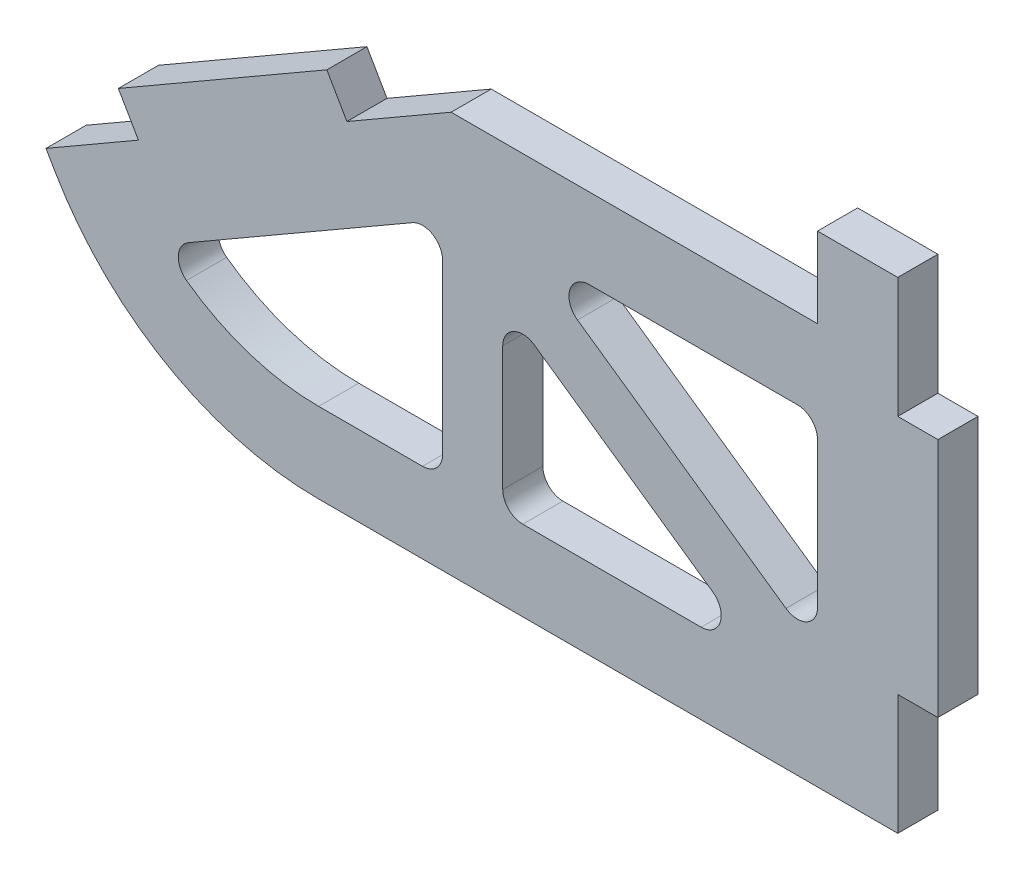
SolidWorks part; units mm, degrees
material "Plain Carbon Steel"
ref_plane "Front Plane" through (0, 0, 0) normal (0, 0, 1) x (1, 0, 0)
ref_plane "Top Plane" through (0, 0, 0) normal (0, 1, 0) x (1, 0, 0)
ref_plane "Right Plane" through (0, 0, 0) normal (1, 0, 0) x (0, 0, -1)
sketch "Sketch1" plane through (0, 0, 0) normal (0, 0, 1) x (1, 0, 0)
  line L1 (0, 0) -> (-152.4, 0)
  line L2 (0, 0) -> (0, -76.2)
  line L3 (0, -76.2) -> (-152.4, -76.2)
  line L4 (-152.4, 0) -> (-152.4, -76.2)
  dimension "D1" = 76.2
  dimension "D2" = 152.4
extrude "Boss-Extrude1" add sketch "Sketch1" along normal blind 6.35
sketch "Sketch2" plane through (0, 0, 6.35) normal (0, 0, 1) x (1, 0, 0)
  line L0 (0, -76.2) -> (0, 0) construction
  line L1 (0, -57.15) -> (6.35, -57.15)
  line L2 (0, -57.15) -> (0, -19.05)
  line L3 (0, -19.05) -> (6.35, -19.05)
  line L4 (6.35, -57.15) -> (6.35, -19.05)
  dimension "D1" = 6.35
  dimension "D2" = 38.1
  dimension "D3" = 19.05
extrude "Boss-Extrude2" add sketch "Sketch2" against normal blind 6.35
sketch "Sketch3" plane through (0, 0, 6.35) normal (0, 0, 1) x (1, 0, 0)
  line L0 (-152.4, -59.8789) -> (-70.6837, -12.7)
  line L1 (-152.4, 0) -> (-152.4, -76.2) construction
  line L3 (-70.6837, -12.7) -> (-12.7, -12.7)
  line L4 (-12.7, -12.7) -> (-12.7, 0)
  line L5 (0, 0) -> (-152.4, 0) construction
  line L6 (-12.7, 0) -> (-152.4, 0)
  line L7 (-152.4, 0) -> (-152.4, -59.8789)
  line L8 (0, -19.05) -> (0, 0) construction
  dimension "D1" = 12.7
  dimension "D2" = 12.7
extrude "Cut-Extrude1" cut sketch "Sketch3" against normal through all
sketch "Sketch4" plane through (0, 0, 6.35) normal (0, 0, 1) x (1, 0, 0)
  line L0 (-152.4, -59.8789) -> (-133.35, -76.2)
  line L1 (-152.4, -76.2) -> (0, -76.2) construction
  line L2 (-133.35, -76.2) -> (-152.4, -76.2)
  line L3 (-152.4, -76.2) -> (-152.4, -59.8789)
  dimension "D1" = 19.05
extrude "Cut-Extrude2" cut sketch "Sketch4" against normal through all
sketch "Sketch5" plane through (0, 0, 6.35) normal (0, 0, 1) x (1, 0, 0)
  line L0 (-87.1815, -22.225) -> (-90.3565, -16.7257)
  line L1 (-152.4, -59.8789) -> (-70.6837, -12.7) construction
  line L3 (-90.3565, -16.7257) -> (-123.3521, -35.7757)
  line L4 (-123.3521, -35.7757) -> (-120.1771, -41.275)
  line L5 (-120.1771, -41.275) -> (-87.1815, -22.225)
  dimension "D1" = 38.1
  dimension "D2" = 19.05
  dimension "D3" = 6.35
extrude "Boss-Extrude3" add sketch "Sketch5" against normal blind 6.35
sketch "Sketch6" plane through (0, 0, 6.35) normal (0, 0, 1) x (1, 0, 0)
  line L0 (-134.8024, -49.7189) -> (-119.5135, -76.2)
  line L1 (-152.4, -59.8789) -> (-120.1771, -41.275) construction
  line L2 (-119.5135, -76.2) -> (-133.35, -76.2)
  line L3 (-133.35, -76.2) -> (-152.4, -59.8789)
  line L4 (-152.4, -59.8789) -> (-134.8024, -49.7189)
  line L5 (-133.35, -76.2) -> (-152.4, -59.8789) construction
  line L6 (-133.35, -76.2) -> (0, -76.2) construction
  dimension "D1" = 20.32
extrude "Cut-Extrude3" cut sketch "Sketch6" against normal through all
fillet "Fillet1" radius 48.26 1 edges at (-119.5135, -76.2, 3.175)
sketch "Sketch7" plane through (0, 0, 6.35) normal (0, 0, 1) x (1, 0, 0)
  line L15 (-102.8286, -45.9235) -> (-91.83, -39.5735)
  line L16 (-12.7, -44.45) -> (-12.7, -31.75)
  line L30 (-91.6506, -63.5) -> (-12.7, -63.5)
  line L31 (-12.7, -63.5) -> (-12.7, -44.45)
  line L32 (-12.7, -44.45) -> (-6.35, -44.45)
  line L33 (-6.35, -44.45) -> (-6.35, -31.75)
  line L34 (-6.35, -31.75) -> (-12.7, -31.75)
  line L35 (-12.7, -31.75) -> (-12.7, -25.4)
  line L36 (-12.7, -25.4) -> (-67.2808, -25.4)
  line L37 (-67.2808, -25.4) -> (-91.83, -39.5735)
  line L38 (-91.83, -39.5735) -> (-95.005, -34.0743)
  line L39 (-95.005, -34.0743) -> (-106.0036, -40.4243)
  line L40 (-106.0036, -40.4243) -> (-102.8286, -45.9235)
  line L41 (-102.8286, -45.9235) -> (-116.2148, -53.6521)
  line L42 (-91.6506, -63.5) -> (-12.7, -63.5)
  line L43 (-12.7, -63.5) -> (-12.7, -44.45)
  line L47 (-12.7, -31.75) -> (-12.7, -25.4)
  line L48 (-12.7, -25.4) -> (-67.2808, -25.4)
  line L49 (-67.2808, -25.4) -> (-91.83, -39.5735)
  line L53 (-102.8286, -45.9235) -> (-116.2148, -53.6521)
  arc A2 (-116.2148, -53.6521) -> (-91.6506, -63.5) centre (-91.6506, -27.94) ccw
  arc A3 (-116.2148, -53.6521) -> (-91.6506, -63.5) centre (-91.6506, -27.94) ccw
  dimension "D1" = 12.7
extrude "Cut-Extrude4" cut sketch "Sketch7" against normal through all
sketch "Sketch8" plane through (0, 0, 6.35) normal (0, 0, 1) x (1, 0, 0)
  line L0 (-12.7, -63.5) -> (-67.2808, -25.4)
  line L1 (-67.2808, -25.4) -> (-67.2808, -63.5)
  line L2 (-91.6506, -63.5) -> (-12.7, -63.5) construction
extrude "Extrude-Thin2" add sketch "Sketch8" against normal up to surface (6.35 mm away) thin up to face at (-60.2993, -46.7645, 0) thin type mid plane wall 9.525
fillet "Fillet2" radius 3.175 9 edges at (-72.0433, -63.5, 3.175) (-116.2148, -53.6521, 3.175) (-72.0433, -28.1496, 3.175) (-12.7, -57.692, 3.175) (-12.7, -25.4, 3.175) (-58.9604, -25.4, 3.175) (-62.5183, -63.5, 3.175) (-21.0204, -63.5, 3.175) (-62.5183, -34.5325, 3.175)
